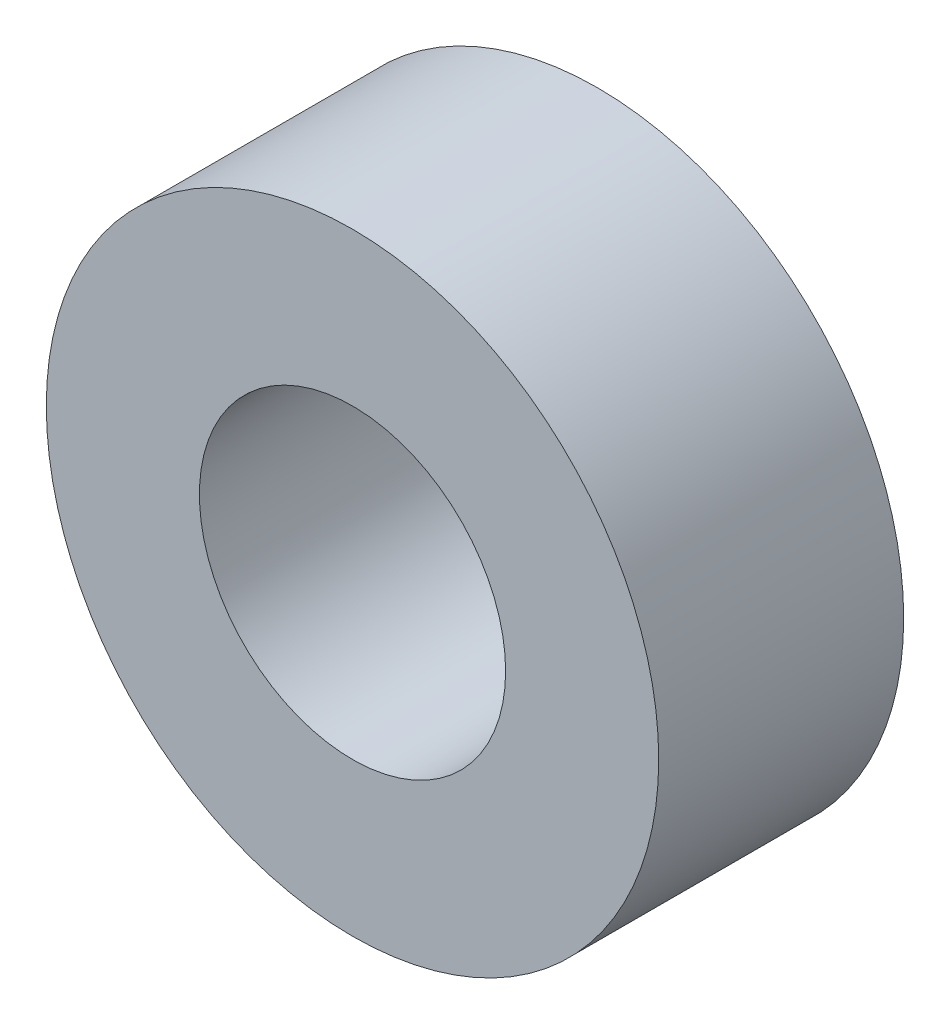
SolidWorks part; units mm, degrees
material "201 Annealed Stainless Steel (SS)"
ref_plane "Front Plane" through (0, 0, 0) normal (0, 0, 1) x (1, 0, 0)
ref_plane "Top Plane" through (0, 0, 0) normal (0, 1, 0) x (1, 0, 0)
ref_plane "Right Plane" through (0, 0, 0) normal (1, 0, 0) x (0, 0, -1)
sketch "Sketch1" plane through (0, 0, 0) normal (0, 0, 1) x (1, 0, 0)
  circle A0 centre (0, 0) radius 2.5
  circle A1 centre (0, 0) radius 5
  dimension "D1" = 10
  dimension "D2" = 5
extrude "Boss-Extrude1" add sketch "Sketch1" along normal blind 4
